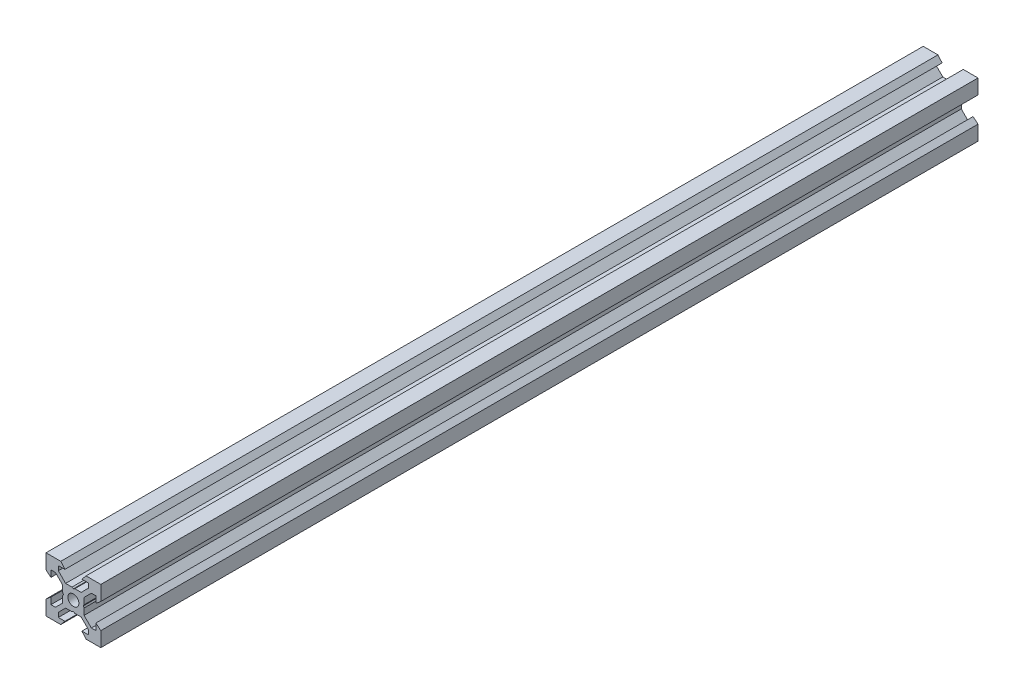
SolidWorks part; units mm, degrees
ref_plane "Front Plane" through (0, 0, 0) normal (0, 0, 1) x (1, 0, 0)
ref_plane "Top Plane" through (0, 0, 0) normal (0, 1, 0) x (1, 0, 0)
ref_plane "Right Plane" through (0, 0, 0) normal (1, 0, 0) x (0, 0, -1)
sketch "Sketch1" plane through (0, 0, 0) normal (0, 0, 1) x (1, 0, 0)
  line L0 (10, 10) -> (4.6104, 10) construction
  line L1 (10, 10) -> (10, 4.6104) construction
  line L2 (10, -10) -> (10, -4.6104) construction
  line L3 (10, -10) -> (4.6104, -10) construction
  line L4 (10, 10) -> (10, 4.6104)
  line L5 (6.5607, 5.5) -> (8.2, 5.5)
  line L6 (5.5, 8.2) -> (5.5, 6.5607)
  line L7 (10, 10) -> (4.6104, 10)
  line L8 (10, 10) -> (10, 4.6104)
  line L9 (6.5607, 5.5) -> (3.9, 2.8393)
  line L10 (5.5, 6.5607) -> (2.8393, 3.9)
  line L11 (10, 4.6104) -> (8.2, 3.1)
  line L12 (4.6104, 10) -> (3.1, 8.2)
  line L13 (8.2, 3.1) -> (8.2, 5.5)
  line L14 (3.1, 8.2) -> (5.5, 8.2)
  line L15 (-6.5607, 5.5) -> (-8.2, 5.5)
  line L16 (6.5607, -5.5) -> (8.2, -5.5)
  line L17 (3.1, -8.2) -> (5.5, -8.2)
  line L18 (8.2, -3.1) -> (8.2, -5.5)
  line L19 (4.6104, -10) -> (3.1, -8.2)
  line L20 (10, -4.6104) -> (8.2, -3.1)
  line L21 (0.5196, -3.9) -> (0, -3.6)
  line L22 (0.5196, 3.9) -> (0, 3.6)
  line L23 (3.6, 0) -> (3.9, -0.5196)
  line L24 (3.9, 0.5196) -> (3.6, 0)
  line L25 (3.9, 0.5196) -> (3.9, 2.8393)
  line L26 (2.8393, 3.9) -> (0.5196, 3.9)
  line L27 (3.9, -2.8393) -> (3.9, -0.5196)
  line L28 (2.8393, -3.9) -> (0.5196, -3.9)
  line L29 (5.5, -6.5607) -> (2.8393, -3.9)
  line L30 (6.5607, -5.5) -> (3.9, -2.8393)
  line L31 (10, -10) -> (10, -4.6104)
  line L32 (10, -10) -> (4.6104, -10)
  line L33 (5.5, -8.2) -> (5.5, -6.5607)
  line L34 (-6.5607, -5.5) -> (-8.2, -5.5)
  line L35 (10, -10) -> (10, -4.6104)
  line L36 (0, 0) -> (0, 8.2) construction
  line L37 (-10, -10) -> (-4.6104, -10) construction
  line L38 (-10, -10) -> (-10, -4.6104) construction
  line L39 (-10, 10) -> (-10, 4.6104) construction
  line L40 (-10, 10) -> (-4.6104, 10) construction
  line L41 (-10, -10) -> (-10, -4.6104)
  line L43 (-5.5, -8.2) -> (-5.5, -6.5607)
  line L44 (-10, -10) -> (-4.6104, -10)
  line L45 (-10, -10) -> (-10, -4.6104)
  line L46 (-6.5607, -5.5) -> (-3.9, -2.8393)
  line L47 (-5.5, -6.5607) -> (-2.8393, -3.9)
  line L48 (-2.8393, -3.9) -> (-0.5196, -3.9)
  line L49 (-3.9, -2.8393) -> (-3.9, -0.5196)
  line L50 (-2.8393, 3.9) -> (-0.5196, 3.9)
  line L51 (-3.9, 0.5196) -> (-3.9, 2.8393)
  line L52 (-3.9, 0.5196) -> (-3.6, 0)
  line L53 (-3.6, 0) -> (-3.9, -0.5196)
  line L54 (-0.5196, 3.9) -> (0, 3.6)
  line L55 (-0.5196, -3.9) -> (0, -3.6)
  line L56 (-10, -4.6104) -> (-8.2, -3.1)
  line L57 (-4.6104, -10) -> (-3.1, -8.2)
  line L58 (-8.2, -3.1) -> (-8.2, -5.5)
  line L59 (-3.1, -8.2) -> (-5.5, -8.2)
  line L60 (-10, -10) -> (10, -10) construction
  line L61 (-10, -10) -> (-10, 10) construction
  line L62 (-3.1, 8.2) -> (-5.5, 8.2)
  line L63 (-8.2, 3.1) -> (-8.2, 5.5)
  line L64 (-4.6104, 10) -> (-3.1, 8.2)
  line L65 (-10, 4.6104) -> (-8.2, 3.1)
  line L66 (-5.5, 6.5607) -> (-2.8393, 3.9)
  line L67 (-6.5607, 5.5) -> (-3.9, 2.8393)
  line L68 (-10, 10) -> (-10, 4.6104)
  line L69 (-10, 10) -> (-4.6104, 10)
  line L70 (-5.5, 8.2) -> (-5.5, 6.5607)
  line L71 (-10, 10) -> (10, 10) construction
  line L72 (-10, 10) -> (-10, 4.6104)
  line L73 (10, -10) -> (10, 10) construction
  line L74 (-10, -10) -> (10, 10) construction
  line L75 (-10, 10) -> (10, -10) construction
  circle A0 centre (0, 0) radius 2
  dimension "D7" = 4
  dimension "D1" = 20
  dimension "D2" = 5.3896
  dimension "D3" = 4.5
  dimension "D4" = 50
  dimension "D5" = 1.8
  dimension "D6" = 1.5104
  dimension "D8" = 5.5
  dimension "D9" = 120
  dimension "D10" = 0.3
  dimension "D11" = 2.3197
  dimension "D12" = 7.8
  dimension "D13" = 7.8
  dimension "D14" = 1.5
  dimension "D15" = 2.6607
extrude "Boss-Extrude1" add sketch "Sketch1" along normal mid plane 320.18 contours L70 L62 L64 L69 L68 L65 L63 L15 L67 L51 L52 L53 L49 L46 L34 L58 L56 L41 L44 L57 L59 L43 L47 L48 L55 L21 L28 L29 L33 L17 L19 L32 L31 L20 L18 L16 L30 L27 L23 L24 L25 L9 L5 L13 L11 L4 L7 L12 L14 L6 L10
